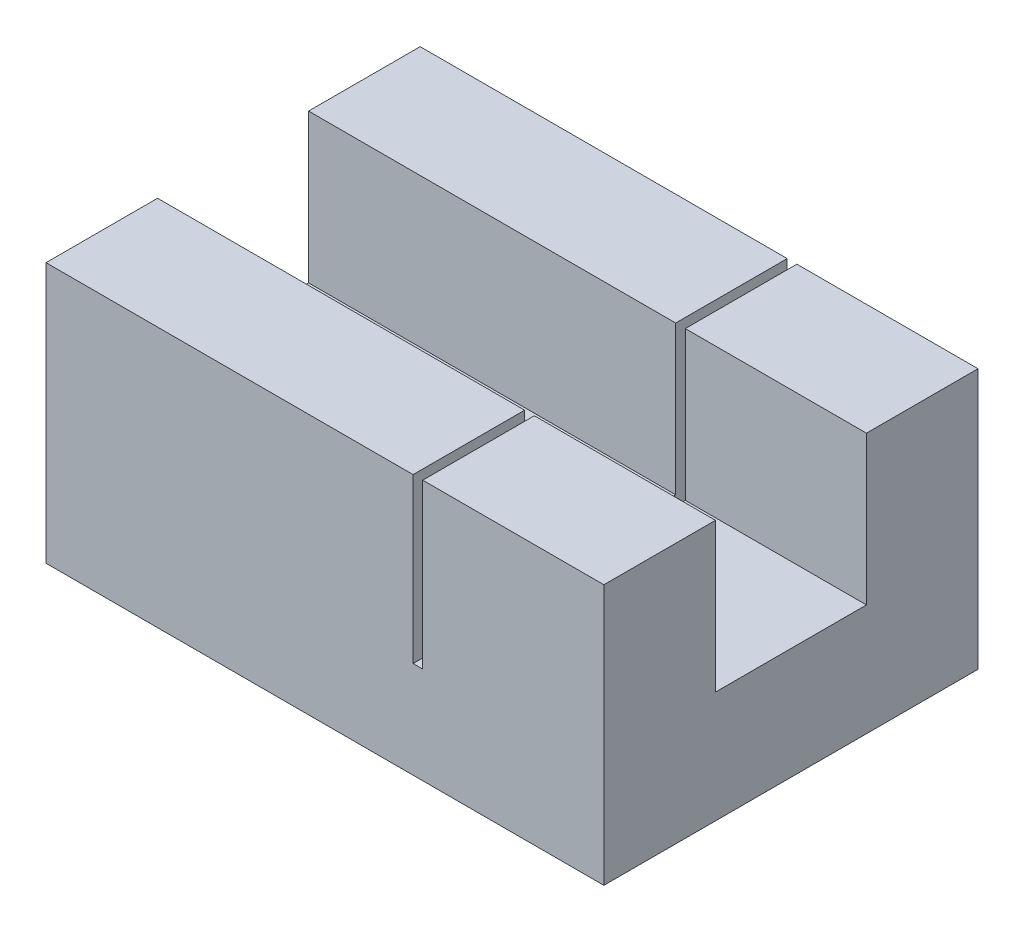
SolidWorks part; units mm, degrees
ref_plane "Front Plane" through (0, 0, 0) normal (0, 0, 1) x (1, 0, 0)
ref_plane "Top Plane" through (0, 0, 0) normal (0, 1, 0) x (1, 0, 0)
ref_plane "Right Plane" through (0, 0, 0) normal (1, 0, 0) x (0, 0, -1)
sketch "Sketch1" plane through (0, 0, 0) normal (0, 1, 0) x (1, 0, 0)
  line L1 (0, 0) -> (50, 0)
  line L2 (0, 0) -> (0, 20.3)
  line L3 (0, 20.3) -> (50, 20.3)
  line L4 (50, 0) -> (50, 20.3)
  dimension "D1" = 20.3
  dimension "D2" = 50
extrude "Boss-Extrude1" add sketch "Sketch1" along normal blind 15
sketch "Sketch2" plane through (0, 0, 0) normal (0, 0, 1) x (1, 0, 0)
  line L1 (0, 0) -> (50, 0)
  line L2 (0, 0) -> (0, 35)
  line L3 (0, 35) -> (50, 35)
  line L4 (50, 0) -> (50, 35)
  dimension "D1" = 35
extrude "Boss-Extrude2" add sketch "Sketch2" along normal blind 15
ref_plane "Plane1" through (0, 0, -10.15) normal (0, 0, -1) x (-1, 0, 0)
mirror "Mirror1" about plane through (0, 0, -10.15) normal (0, 0, -1) of "Boss-Extrude2"
sketch "Sketch3" plane through (0, 35, 0) normal (0, 1, 0) x (1, 0, 0)
  line L0 (50, 35.3) -> (0, 35.3) construction
  line L1 (24.35, 35.3) -> (25.65, 35.3)
  line L2 (24.35, 35.3) -> (24.35, -15)
  line L3 (24.35, -15) -> (25.65, -15)
  line L4 (25.65, 35.3) -> (25.65, -15)
  line L5 (50, -15) -> (0, -15) construction
  line L6 (25, -15) -> (0, -15) construction
  line L7 (25, -15) -> (50, -15) construction
  dimension "D1" = 1.3
extrude "Cut-Extrude1" cut sketch "Sketch3" against normal offset from surface (22 mm away) 13 up to face at (25, 0, -10.15)
sketch "Sketch4" plane through (0, 0, 0) normal (-1, 0, 0) x (0, 0, 1)
  line L8 (-35.3, 0) -> (15, 0)
  line L9 (15, 0) -> (15, 35)
  line L10 (15, 35) -> (0, 35)
  line L11 (0, 35) -> (0, 15)
  line L12 (0, 15) -> (-20.3, 15)
  line L13 (-20.3, 15) -> (-20.3, 35)
  line L14 (-20.3, 35) -> (-35.3, 35)
  line L15 (-35.3, 35) -> (-35.3, 0)
  line L16 (-35.3, 0) -> (15, 0)
  line L17 (15, 0) -> (15, 35)
  line L18 (15, 35) -> (0, 35)
  line L19 (0, 35) -> (0, 15)
  line L20 (0, 15) -> (-20.3, 15)
  line L21 (-20.3, 15) -> (-20.3, 35)
  line L22 (-20.3, 35) -> (-35.3, 35)
  line L23 (-35.3, 35) -> (-35.3, 0)
  dimension "D1" = 0
extrude "Boss-Extrude3" add sketch "Sketch4" along normal blind 25
ref_plane "Plane2" through (15.2137, 0, 0) normal (1, 0, 0) x (0, 0, -1)
ref_plane "Plane3" through (35.3334, 0, 0) normal (1, 0, 0) x (0, 0, -1)
ref_plane "Plane4" through (0, 10.4442, 0) normal (0, 1, 0) x (1, 0, 0)
ref_plane "Plane5" through (0, 21.8337, 0) normal (0, 1, 0) x (1, 0, 0)
split "Split1" bodies to split 104 resulting bodies 118
